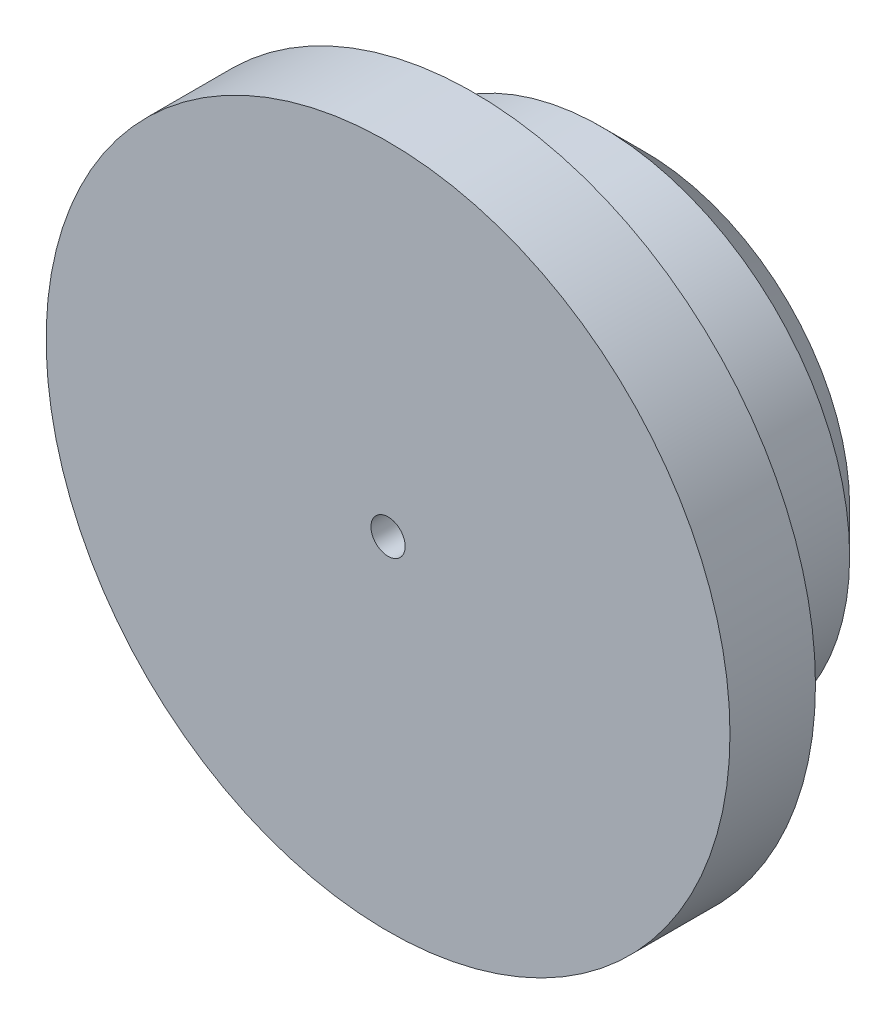
SolidWorks part; units mm, degrees
ref_plane "Plan de face" through (0, 0, 0) normal (0, 0, 1) x (1, 0, 0)
ref_plane "Plan de dessus" through (0, 0, 0) normal (0, 1, 0) x (1, 0, 0)
ref_plane "Plan de droite" through (0, 0, 0) normal (1, 0, 0) x (0, 0, -1)
sketch "Esquisse1" plane through (0, 0, 0) normal (0, 0, 1) x (1, 0, 0)
  circle A0 centre (0, 0) radius 29
extrude "Boss.-Extru.1" add sketch "Esquisse1" along normal blind 20
sketch "Esquisse2" plane through (0, 0, 20) normal (0, 0, 1) x (1, 0, 0)
  circle A0 centre (0, 0) radius 40
extrude "Boss.-Extru.2" add sketch "Esquisse2" along normal blind 10
chamfer "Chanfrein1" distance 5 angle 45 1 edges at (29, 0, 0)
sketch "Esquisse3" plane through (0, 0, 30) normal (0, 0, 1) x (1, 0, 0)
  circle A0 centre (0, 0) radius 2
extrude "Enlèv. mat.-Extru.1" cut sketch "Esquisse3" against normal up to surface (30 mm away) up to face at (24, 0, 0)
sketch "Esquisse4" plane through (0, 0, 0) normal (0, 0, -1) x (-1, 0, 0)
  line L1 (2.5, 10) -> (-2.5, 10)
  line L3 (-2.5, -10) -> (2.5, -10)
  line L5 (-2.5, 3) -> (2.5, 3)
  line L7 (-2.5, -3) -> (2.5, -3)
  line L8 (-2.5, 10) -> (-2.5, 3)
  line L9 (2.5, 3) -> (2.5, 10)
  line L10 (-2.5, -3) -> (-2.5, -10)
  line L11 (2.5, -3) -> (2.5, -10)
extrude "Boss.-Extru.4" add sketch "Esquisse4" along normal blind 10
